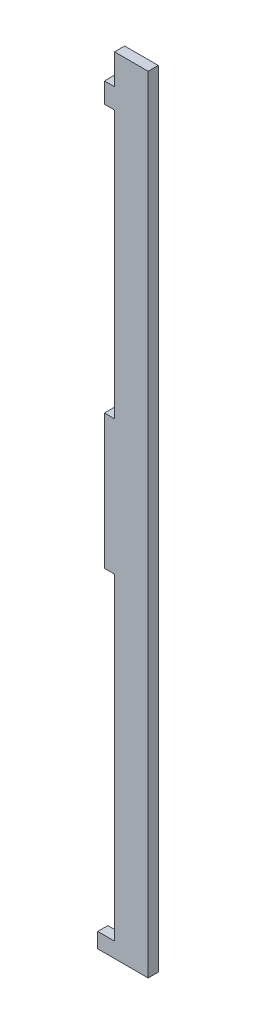
SolidWorks part; units mm, degrees
material "Acrylic (Medium-high impact)"
ref_plane "Front Plane" through (0, 0, 0) normal (0, 0, 1) x (1, 0, 0)
ref_plane "Top Plane" through (0, 0, 0) normal (0, 1, 0) x (1, 0, 0)
ref_plane "Right Plane" through (0, 0, 0) normal (1, 0, 0) x (0, 0, -1)
sketch "Sketch1" plane through (0, 0, 0) normal (0, 0, 1) x (1, 0, 0)
  line L0 (-10, 109.7971) -> (-10, 105.2971) construction
  line L1 (-10, 99.2971) -> (-10, 19.7971) construction
  line L2 (-10, -20.2029) -> (-10, -110.2029) construction
  line L3 (0, 109.7971) -> (0, -114.7029) construction
  line L4 (-10.5, -114.7029) -> (-15, -114.7029) construction
  line L5 (0, -114.7029) -> (0, -119.2029) construction
  line L6 (0, -119.2029) -> (-15, -119.2029) construction
  line L7 (-15, -119.2029) -> (-15, -114.7029) construction
  line L8 (-15, -114.7029) -> (-10, -114.7029) construction
  line L9 (-10, -114.7029) -> (-10, -110.2029) construction
  line L10 (-10, 109.7971) -> (-10, 114.2971) construction
  line L11 (-10, 114.2971) -> (0, 114.2971) construction
  line L12 (0, 114.2971) -> (0, 109.7971) construction
  line L13 (-10, 19.7971) -> (-12, 19.7971) construction
  line L14 (-10, 105.2971) -> (-13, 105.2971) construction
  line L15 (-13, 105.2971) -> (-13, 99.2971) construction
  line L16 (-13, 99.2971) -> (-10, 99.2971) construction
  line L17 (-10, 19.7971) -> (-13, 19.7971) construction
  line L18 (-13, 19.7971) -> (-13, -20.2029) construction
  line L19 (-13, -20.2029) -> (-10, -20.2029) construction
sketch "Sketch2" plane through (0, 0, 0) normal (0, 0, 1) x (1, 0, 0)
  line L0 (-10, 114.2971) -> (0, 114.2971) construction
  line L1 (-13, 99.2971) -> (-10, 99.2971) construction
  line L2 (-13, 105.2971) -> (-13, 99.2971) construction
  line L3 (-10, 105.2971) -> (-13, 105.2971) construction
  line L4 (-15, -119.2029) -> (-15, -114.7029) construction
  line L5 (0, -119.2029) -> (-15, -119.2029) construction
  line L6 (-13, -20.2029) -> (-10, -20.2029) construction
  line L7 (-13, 19.7971) -> (-13, -20.2029) construction
  line L8 (-10, 99.2971) -> (-10, 19.7971) construction
  line L9 (-10, 114.2971) -> (0, 114.2971)
  line L10 (-13, 99.2971) -> (-10, 99.2971)
  line L11 (-13, 105.2971) -> (-13, 99.2971)
  line L12 (-10, 105.2971) -> (-13, 105.2971)
  line L13 (-15, -119.2029) -> (-15, -114.7029)
  line L14 (0, -119.2029) -> (-15, -119.2029)
  line L15 (-13, -20.2029) -> (-10, -20.2029)
  line L16 (-13, 19.7971) -> (-13, -20.2029)
  line L17 (-10, 99.2971) -> (-10, 19.7971)
  line L18 (-10, 105.2971) -> (-10, 114.2971)
  line L19 (0, 114.2971) -> (0, -119.2029)
  line L20 (-15, -114.7029) -> (-10, -114.7029)
  line L21 (-10, -114.7029) -> (-10, -20.2029)
  line L22 (-13, 19.7971) -> (-10, 19.7971)
extrude "Boss-Extrude1" add sketch "Sketch2" along normal blind 3
